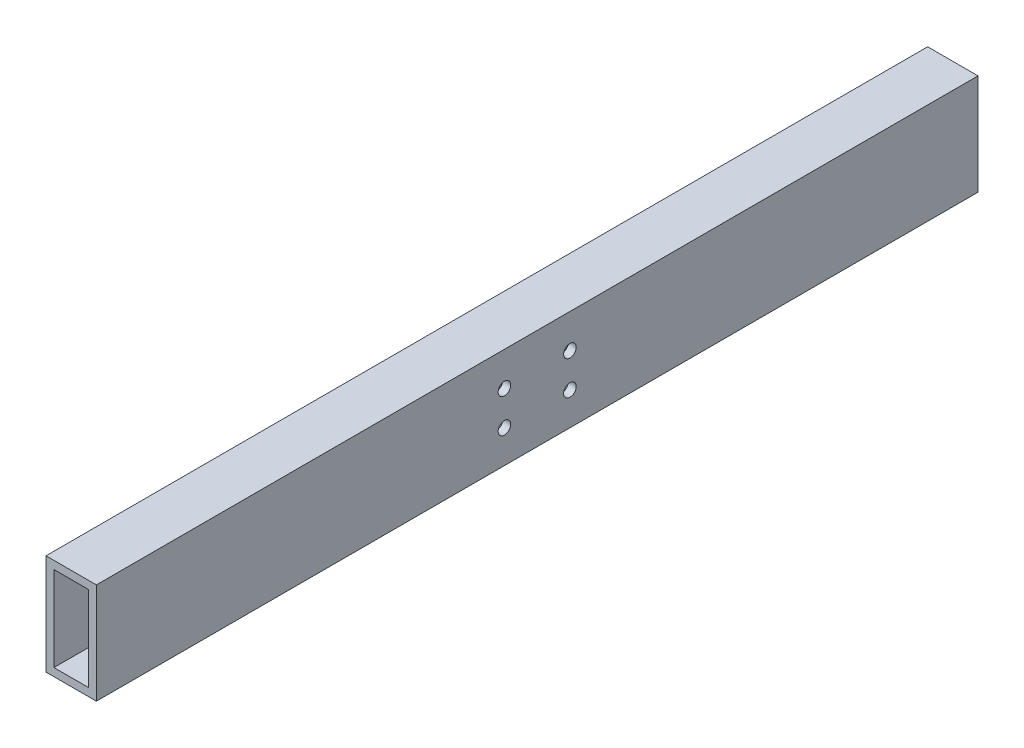
SolidWorks part; units mm, degrees
material "1.0037 (S235JR)"
ref_plane "Front Plane" through (0, 0, 0) normal (0, 0, 1) x (1, 0, 0)
ref_plane "Top Plane" through (0, 0, 0) normal (0, 1, 0) x (1, 0, 0)
ref_plane "Right Plane" through (0, 0, 0) normal (1, 0, 0) x (0, 0, -1)
curve "Curve1"
  spline degree 1 poles (0, 0, -350) (0, 0, 350) knots 0 0 1 1
sketch "Sketch1" plane through (0, 0, 0) normal (0, 0, 1) x (1, 0, 0)
  line L0 (0, 35.3535) -> (0, -33.8384) construction
  line L1 (-20, 40) -> (20, 40)
  line L2 (-20, 40) -> (-20, -40)
  line L3 (-20, -40) -> (20, -40)
  line L4 (20, 40) -> (20, -40)
  line L5 (-13.7, 33.7) -> (13.7, 33.7)
  line L6 (-13.7, 33.7) -> (-13.7, -33.7)
  line L7 (-13.7, -33.7) -> (13.7, -33.7)
  line L8 (13.7, 33.7) -> (13.7, -33.7)
  line L9 (-39.3939, 0) -> (41.5152, 0) construction
  dimension "D1" = 40
  dimension "D2" = 27.4
  dimension "D3" = 80
  dimension "D4" = 67.4
sweep "Sweep1" add profiles "Sketch1" path "Curve1"
sketch "Sketch2" plane through (20, 0, 0) normal (1, 0, 0) x (0, 0, -1)
  line L0 (26, 88.4507) -> (26, -117.3154) construction
  line L1 (-350, 40) -> (350, 40) construction
  point P3 (26, 13)
  point P4 (26, -14)
  dimension "D1" = 27
  dimension "D2" = 27
  dimension "D5" = 26
hole_wizard "M8 Clearance Hole1" positions "Sketch3" profile "Sketch5" hole size "M8" standard "ISO" end condition through all
sketch "Sketch3" plane through (20, 0, 0) normal (1, 0, 0) x (0, 0, -1)
  point P0 (26, 13)
  point P3 (26, -14)
sketch "Sketch5" plane through (20, 13, -26) normal (0, 1, 0) x (0, 0, -1)
  line L0 (0, 0) -> (0, 40)
  line L1 (0, 40) -> (5, 40)
  line L2 (5, 40) -> (5, 0)
  line L5 (5, 0) -> (0, 0)
  line L11 (0, -6.35) -> (0, 107.95) construction
  dimension "Thru Hole Dia." = 10
  dimension "Thru Hole Depth" = 40
mirror "Mirror1" about plane through (0, 0, 0) normal (0, 0, 1) of "M8 Clearance Hole1"
